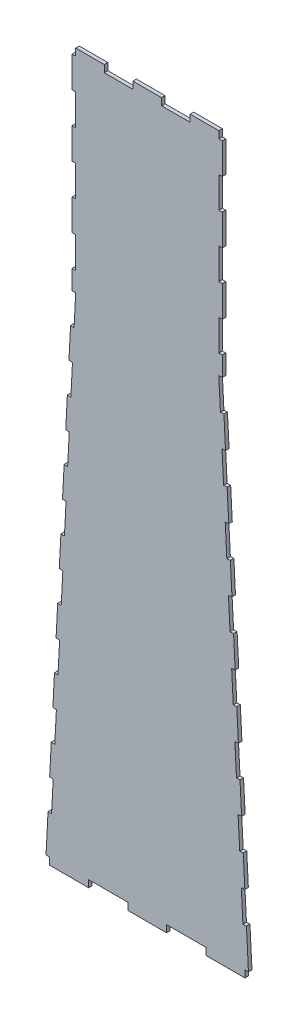
SolidWorks part; units mm, degrees
ref_plane "Front Plane" through (0, 0, 0) normal (0, 0, 1) x (1, 0, 0)
ref_plane "Top Plane" through (0, 0, 0) normal (0, 1, 0) x (1, 0, 0)
ref_plane "Right Plane" through (0, 0, 0) normal (1, 0, 0) x (0, 0, -1)
sketch "Sketch4" plane through (0, 0, 0) normal (0, 0, 1) x (1, 0, 0)
  line L4 (-215.8818, 2072.64) -> (-215.8818, 1463.04) construction
  line L5 (-215.8818, 1463.04) -> (-292.1, 0) construction
  line L13 (-292.1, 0) -> (292.1, 0) construction
  line L17 (-215.8818, 2072.64) -> (215.8818, 2072.64) construction
  line L22 (-220.5068, 1374.2604) -> (-225.1319, 1285.4808)
  line L25 (-205.7153, 2072.64) -> (-123.444, 2072.64)
  line L26 (-123.444, 2052.32) -> (-123.444, 2072.64)
  line L27 (-123.444, 2052.32) -> (-123.444, 2072.64)
  line L28 (-41.1356, 2072.64) -> (-41.1356, 2052.32)
  line L29 (-41.1356, 2072.64) -> (41.1356, 2072.64)
  line L30 (0, 2072.64) -> (0, 0) construction
  line L31 (262.1322, 575.2439) -> (266.7573, 486.4643) construction
  line L33 (-280.8749, 20.32) -> (280.8749, 20.32)
  line L34 (280.6324, 220.1255) -> (285.2574, 131.3459) construction
  line L35 (271.3823, 397.6847) -> (276.0073, 308.9051) construction
  line L36 (243.632, 930.3623) -> (248.2571, 841.5827) construction
  line L37 (252.8821, 752.8031) -> (257.5072, 664.0235) construction
  line L38 (-205.7153, 2072.64) -> (-123.444, 2072.64) construction
  line L39 (-123.4193, 2072.64) -> (-41.148, 2072.64) [skipped]
  line L40 (41.1727, 2072.64) -> (123.444, 2072.64) [skipped]
  line L41 (-205.7153, 2072.64) -> (-205.7153, 1963.42)
  line L42 (-205.7153, 1963.42) -> (-215.8818, 1963.42)
  line L43 (-215.8818, 2052.32) -> (-215.8818, 1963.42)
  line L44 (-205.7153, 1963.42) -> (-215.8818, 1963.42)
  line L45 (-205.7153, 1874.52) -> (-215.8818, 1874.52)
  line L46 (-215.8818, 1874.52) -> (-215.8818, 1785.62)
  line L47 (-205.7153, 1874.52) -> (-215.8818, 1874.52)
  line L48 (-205.7153, 1785.62) -> (-215.8818, 1785.62)
  line L49 (-220.5068, 1374.2604) -> (-210.3679, 1373.7322)
  line L50 (-205.7153, 1785.62) -> (-215.8818, 1785.62)
  line L51 (-205.7153, 1696.72) -> (-215.8818, 1696.72)
  line L52 (-215.8818, 1696.72) -> (-215.8818, 1607.82)
  line L53 (-205.7153, 1696.72) -> (-215.8818, 1696.72)
  line L54 (-205.7153, 1607.82) -> (-215.8818, 1607.82)
  line L55 (-225.1319, 1285.4808) -> (-214.9929, 1284.9526)
  line L56 (-205.7153, 1607.82) -> (-215.8818, 1607.82)
  line L57 (-205.7153, 1518.92) -> (-215.8818, 1518.92)
  line L58 (-215.8818, 1518.92) -> (-215.8818, 1463.04)
  line L59 (-205.7153, 1518.92) -> (-215.8818, 1518.92)
  line L60 (-215.8818, 1463.04) -> (-205.7153, 1463.04)
  line L61 (234.382, 1107.9216) -> (239.007, 1019.142) construction
  line L62 (-215.8818, 1463.04) -> (-205.7153, 1463.04) construction
  line L63 (-205.7153, 1463.04) -> (-205.7153, 2072.64)
  line L64 (-205.7153, 1463.04) -> (-280.8749, 20.32)
  line L65 (215.8818, 1463.04) -> (220.5068, 1374.2604) construction
  line L66 (225.1319, 1285.4808) -> (229.7569, 1196.7012) construction
  line L67 (215.8818, 1463.04) -> (205.7153, 1463.04) construction
  line L68 (-220.5068, 1374.2604) -> (-210.3679, 1373.7322)
  line L69 (-215.8818, 1607.82) -> (-215.8818, 1518.92) [skipped]
  line L70 (-215.8818, 1785.62) -> (-215.8818, 1696.72) [skipped]
  line L71 (-215.8818, 1963.42) -> (-215.8818, 1874.52) [skipped]
  line L72 (-210.3679, 1373.7322) -> (-214.9929, 1284.9526)
  line L73 (-225.1319, 1285.4808) -> (-229.7569, 1196.7012) construction
  line L74 (-225.1319, 1285.4808) -> (-214.9993, 1284.9529)
  line L75 (-229.7569, 1196.7012) -> (-219.6179, 1196.173)
  line L76 (-215.8818, 1463.04) -> (-220.5068, 1374.2604) construction
  line L77 (-229.7569, 1196.7012) -> (-219.6179, 1196.173)
  line L78 (-229.7569, 1196.7012) -> (-234.382, 1107.9216)
  line L79 (-234.382, 1107.9216) -> (-239.007, 1019.142) construction
  line L80 (-234.382, 1107.9216) -> (-224.243, 1107.3934)
  line L81 (-239.007, 1019.142) -> (-228.868, 1018.6138)
  line L82 (-257.5072, 664.0235) -> (-247.3682, 663.4953)
  line L83 (-248.2571, 841.5827) -> (-252.8821, 752.8031)
  line L84 (-243.632, 930.3623) -> (-233.4931, 929.8341)
  line L85 (-239.007, 1019.142) -> (-228.8744, 1018.6141)
  line L86 (-252.8821, 752.8031) -> (-257.5072, 664.0235) construction
  line L87 (-252.8821, 752.8031) -> (-242.7432, 752.2749)
  line L88 (-239.007, 1019.142) -> (-243.632, 930.3623)
  line L89 (-243.632, 930.3623) -> (-248.2571, 841.5827) construction
  line L90 (-248.2571, 841.5827) -> (-238.1181, 841.0545)
  line L91 (-271.3823, 397.6847) -> (-261.2433, 397.1565)
  line L92 (-271.3823, 397.6847) -> (-276.0073, 308.9051) construction
  line L93 (-280.8749, 20.32) -> (-291.0414, 20.32)
  line L94 (-280.6324, 220.1255) -> (-285.2574, 131.3459) construction
  line L95 (-285.2574, 131.3459) -> (-291.0414, 20.32)
  line L96 (-280.8749, 20.32) -> (-280.8749, 0)
  line L97 (-285.2574, 131.3459) -> (-275.1185, 130.8177)
  line L98 (-266.7573, 486.4643) -> (-271.3823, 397.6847)
  line L99 (-262.1322, 575.2439) -> (-251.9932, 574.7157)
  line L100 (-276.0073, 308.9051) -> (-265.8684, 308.3769)
  line L101 (-257.5072, 664.0235) -> (-247.3746, 663.4957)
  line L102 (-276.0073, 308.9051) -> (-280.6324, 220.1255)
  line L103 (-257.5072, 664.0235) -> (-262.1322, 575.2439)
  line L104 (-168.3021, 20.32) -> (-168.3021, 0)
  line L105 (-262.1322, 575.2439) -> (-266.7573, 486.4643) construction
  line L106 (-266.7573, 486.4643) -> (-256.6183, 485.9361)
  line L107 (-280.6324, 220.1255) -> (-270.4934, 219.5973)
  line L108 (-205.7218, 1430.02) -> (-205.9939, 1430.02) [skipped]
  line L109 (205.7153, 2072.64) -> (123.444, 2072.64) construction
  line L110 (-168.3021, 20.32) -> (-168.3021, 0)
  line L111 (-55.7293, 20.32) -> (-55.7293, 0)
  line L112 (-55.7293, 20.32) -> (-55.7293, 0)
  line L117 (-205.7153, 2052.32) -> (0.0215, 2052.32)
  line L118 (-55.7293, 0) -> (55.7293, 0)
  line L120 (-280.8749, 0) -> (-168.3021, 0)
  line L121 (215.8818, 1463.04) -> (292.1, 0) construction
  line L122 (215.8818, 2072.64) -> (215.8818, 1463.04) construction
  line L123 (-215.8818, 2052.32) -> (-205.7153, 2052.32)
  line L124 (0, -55) -> (0, 55) construction
  line L125 (215.8818, 2052.32) -> (205.7153, 2052.32)
  line L126 (280.8749, 0) -> (168.3021, 0)
  line L127 (205.7153, 2052.32) -> (-0.0215, 2052.32)
  line L128 (55.7293, 20.32) -> (55.7293, 0)
  line L129 (55.7293, 20.32) -> (55.7293, 0)
  line L130 (168.3021, 20.32) -> (168.3021, 0)
  line L131 (280.6324, 220.1255) -> (270.4934, 219.5973)
  line L132 (266.7573, 486.4643) -> (256.6183, 485.9361)
  line L133 (168.3021, 20.32) -> (168.3021, 0)
  line L134 (257.5072, 664.0235) -> (262.1322, 575.2439)
  line L137 (276.0073, 308.9051) -> (280.6324, 220.1255)
  line L138 (257.5072, 664.0235) -> (247.3746, 663.4957)
  line L139 (276.0073, 308.9051) -> (265.8684, 308.3769)
  line L140 (262.1322, 575.2439) -> (251.9932, 574.7157)
  line L141 (266.7573, 486.4643) -> (271.3823, 397.6847)
  line L142 (285.2574, 131.3459) -> (275.1185, 130.8177)
  line L143 (280.8749, 20.32) -> (280.8749, 0)
  line L144 (285.2574, 131.3459) -> (291.0414, 20.32)
  line L145 (280.8749, 20.32) -> (291.0414, 20.32)
  line L146 (271.3823, 397.6847) -> (261.2433, 397.1565)
  line L147 (248.2571, 841.5827) -> (238.1181, 841.0545)
  line L148 (239.007, 1019.142) -> (243.632, 930.3623)
  line L149 (252.8821, 752.8031) -> (242.7432, 752.2749)
  line L150 (239.007, 1019.142) -> (228.8744, 1018.6141)
  line L151 (243.632, 930.3623) -> (233.4931, 929.8341)
  line L152 (248.2571, 841.5827) -> (252.8821, 752.8031)
  line L153 (257.5072, 664.0235) -> (247.3682, 663.4953)
  line L154 (239.007, 1019.142) -> (228.868, 1018.6138)
  line L155 (234.382, 1107.9216) -> (224.243, 1107.3934)
  line L156 (229.7569, 1196.7012) -> (234.382, 1107.9216)
  line L157 (229.7569, 1196.7012) -> (219.6179, 1196.173)
  line L158 (229.7569, 1196.7012) -> (219.6179, 1196.173)
  line L159 (225.1319, 1285.4808) -> (214.9993, 1284.9529)
  line L160 (210.3679, 1373.7322) -> (214.9929, 1284.9526)
  line L163 (220.5068, 1374.2604) -> (210.3679, 1373.7322)
  line L164 (205.7153, 1463.04) -> (280.8749, 20.32)
  line L166 (205.7153, 1463.04) -> (205.7153, 2072.64)
  line L167 (215.8818, 1463.04) -> (205.7153, 1463.04)
  line L168 (205.7153, 1518.92) -> (215.8818, 1518.92)
  line L170 (215.8818, 1518.92) -> (215.8818, 1463.04)
  line L173 (205.7153, 1518.92) -> (215.8818, 1518.92)
  line L176 (205.7153, 1607.82) -> (215.8818, 1607.82)
  line L182 (225.1319, 1285.4808) -> (214.9929, 1284.9526)
  line L184 (205.7153, 1607.82) -> (215.8818, 1607.82)
  line L185 (205.7153, 1696.72) -> (215.8818, 1696.72)
  line L186 (215.8818, 1696.72) -> (215.8818, 1607.82)
  line L187 (205.7153, 1696.72) -> (215.8818, 1696.72)
  line L188 (205.7153, 1785.62) -> (215.8818, 1785.62)
  line L189 (220.5068, 1374.2604) -> (210.3679, 1373.7322)
  line L190 (205.7153, 1785.62) -> (215.8818, 1785.62)
  line L191 (281.9891, 20.32) -> (281.9891, 0) [skipped]
  line L192 (205.7153, 1874.52) -> (215.8818, 1874.52)
  line L193 (205.74, 2052.32) -> (205.74, 2072.64) [skipped]
  line L194 (123.444, 2052.32) -> (123.444, 2072.64) [skipped]
  line L195 (41.148, 2052.32) -> (41.148, 2072.64) [skipped]
  line L198 (-41.148, 2052.32) -> (-41.148, 2072.64) [skipped]
  line L200 (123.4687, 2072.64) -> (205.74, 2072.64) [skipped]
  line L201 (169.4163, 20.32) -> (169.4163, 0) [skipped]
  line L202 (169.4163, 20.32) -> (169.4163, 0) [skipped]
  line L203 (56.8435, 20.32) -> (56.8435, 0) [skipped]
  line L204 (56.8435, 20.32) -> (56.8435, 0) [skipped]
  line L205 (215.8818, 1874.52) -> (215.8818, 1785.62)
  line L206 (205.7153, 1874.52) -> (215.8818, 1874.52)
  line L207 (205.7153, 1963.42) -> (215.8818, 1963.42)
  line L208 (215.8818, 2052.32) -> (215.8818, 1963.42)
  line L209 (205.7153, 1963.42) -> (215.8818, 1963.42)
  line L210 (205.7153, 2072.64) -> (205.7153, 1963.42)
  line L211 (41.1356, 2072.64) -> (41.1356, 2052.32)
  line L212 (123.444, 2052.32) -> (123.444, 2072.64)
  line L213 (123.444, 2052.32) -> (123.444, 2072.64)
  line L214 (205.7153, 2072.64) -> (123.444, 2072.64)
  line L216 (220.5068, 1374.2604) -> (225.1319, 1285.4808)
  point P159 (0, 20.32)
  point P162 (205.7153, 2078.4375)
  point P163 (205.7153, 2084.9765)
  point P164 (0, 0)
  point P165 (0, 0)
  point P166 (0, 0)
  point P167 (0, 0)
  dimension "D2" = 88.9
  dimension "D3" = 41.1356
  dimension "D4" = 609.6
  dimension "D5" = 2072.64
  dimension "D6" = 10.1665
  dimension "D9" = 20.32
  dimension "D10" = 205.7153
  dimension "D13" = 88.9
  dimension "D14" = 112.5728
  dimension "D15" = 5
  dimension "D16" = 20.32
  dimension "D7" = 10.1527
  dimension "D11" = 5
  dimension "D12" = 7
extrude "Boss-Extrude3" add sketch "Sketch4" along normal blind 10.16
